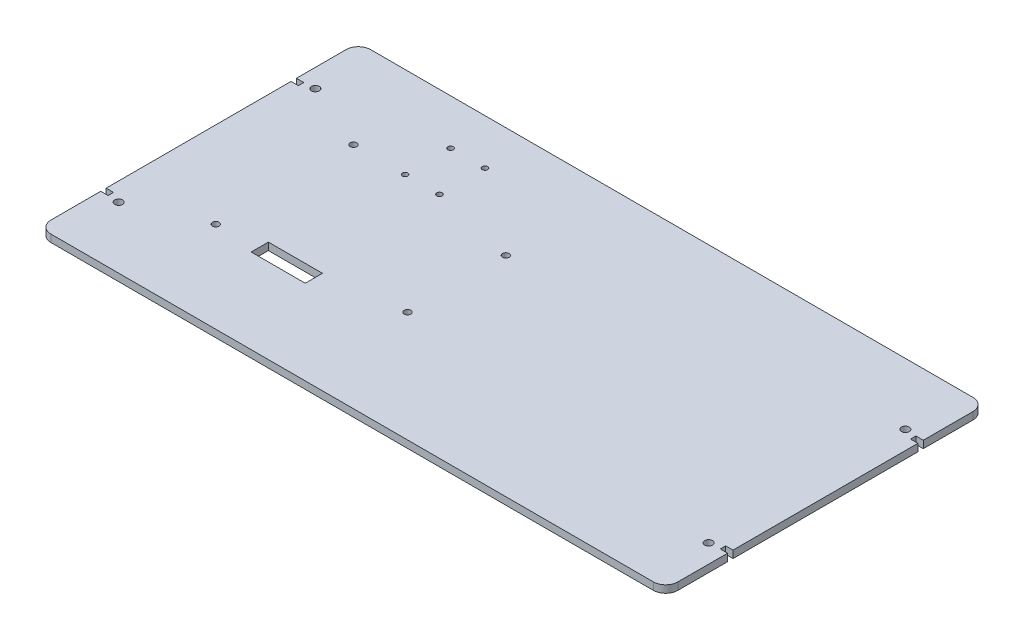
SolidWorks part; units mm, degrees
material "Acrylic (Medium-high impact)"
ref_plane "Front Plane" through (0, 0, 0) normal (0, 0, 1) x (1, 0, 0)
ref_plane "Top Plane" through (0, 0, 0) normal (0, 1, 0) x (1, 0, 0)
ref_plane "Right Plane" through (0, 0, 0) normal (1, 0, 0) x (0, 0, -1)
sketch "Sketch1" plane through (0, 0, 0) normal (0, 1, 0) x (1, 0, 0)
  line L0 (-127.5, 0) -> (127.5, 0) construction
  line L1 (-127.5, -65) -> (127.5, -65) construction
  line L2 (-127.5, -65) -> (-127.5, 65) construction
  line L3 (-127.5, 65) -> (127.5, 65) construction
  line L4 (127.5, -65) -> (127.5, 65) construction
  line L5 (-127.5, -65) -> (127.5, 65) construction
  line L6 (-127.5, 65) -> (127.5, -65) construction
  line L7 (0, 65) -> (0, -65) construction
  line L8 (-75.5, -23.6) -> (-53.5, -23.6)
  line L9 (-75.5, -23.6) -> (-75.5, -30.6)
  line L10 (-75.5, -30.6) -> (-53.5, -30.6)
  line L11 (-53.5, -23.6) -> (-53.5, -30.6)
  line L12 (-75.5, -23.6) -> (-53.5, -30.6) construction
  line L13 (-75.5, -30.6) -> (-53.5, -23.6) construction
  line L14 (-64.5, -27.1) -> (-64.5, 65) construction
  line L22 (-127.5, 65) -> (127.5, 65)
  line L25 (127.5, -65) -> (-127.5, -65)
  line L27 (-127.5, 39.8) -> (-124.5, 39.8)
  line L28 (-124.5, 39.8) -> (-124.5, 37.6)
  line L29 (-124.5, 37.6) -> (-127.5, 37.6)
  line L30 (-124.5, -37.6) -> (-127.5, -37.6)
  line L31 (-124.5, -39.8) -> (-124.5, -37.6)
  line L32 (-127.5, -39.8) -> (-124.5, -39.8)
  line L33 (-127.5, 65) -> (-127.5, 39.8)
  line L34 (-127.5, 37.6) -> (-127.5, -37.6)
  line L35 (-127.5, -39.8) -> (-127.5, -65)
  line L36 (127.5, -39.8) -> (127.5, -65)
  line L37 (127.5, -39.8) -> (124.5, -39.8)
  line L38 (124.5, -39.8) -> (124.5, -37.6)
  line L39 (124.5, -37.6) -> (127.5, -37.6)
  line L40 (127.5, 37.6) -> (127.5, -37.6)
  line L41 (124.5, 37.6) -> (127.5, 37.6)
  line L42 (124.5, 39.8) -> (124.5, 37.6)
  line L43 (127.5, 39.8) -> (124.5, 39.8)
  line L44 (127.5, 65) -> (127.5, 39.8)
  circle A0 centre (-92.5, 28) radius 1.35
  circle A1 centre (-22.5, 20) radius 1.35
  circle A2 centre (-92.5, -28) radius 1.35
  circle A3 centre (-22.5, -20) radius 1.35
  circle A4 centre (-120, 40) radius 1.6
  circle A5 centre (120, 40) radius 1.6
  circle A6 centre (120, -40) radius 1.6
  circle A7 centre (-120, -40) radius 1.6
  circle A21 centre (-71.5, 46.5) radius 1.1
  circle A22 centre (-71.5, 28) radius 1.1
  circle A23 centre (-57.5, 46.5) radius 1.1
  circle A24 centre (-57.5, 28) radius 1.1
  point P0 (0, 0)
  point P16 (-64.5, -27.1)
  dimension "D3" = 2.7
  dimension "D5" = 2.7
  dimension "D13" = 3.2
  dimension "D16" = 2.2
  dimension "D17" = 3
  dimension "D18" = 37.6
  dimension "D24" = 2.2
  dimension "D26" = 2.2
  dimension "D1" = 130
  dimension "D2" = 255
  dimension "D4" = 28
  dimension "D6" = 70
  dimension "D7" = 8
  dimension "D8" = 92.5
  dimension "D9" = 7
  dimension "D10" = 22
  dimension "D11" = 28
  dimension "D12" = 0.9
  dimension "D14" = 7.5
  dimension "D15" = 40
  dimension "D25" = 7
  dimension "D27" = 18.5
extrude "Boss-Extrude1" add sketch "Sketch1" along normal blind 3
fillet "Fillet1" radius 5 4 edges at (127.5, 1.5, 65) (127.5, 1.5, -65) (-127.5, 1.5, 65) (-127.5, 1.5, -65)
